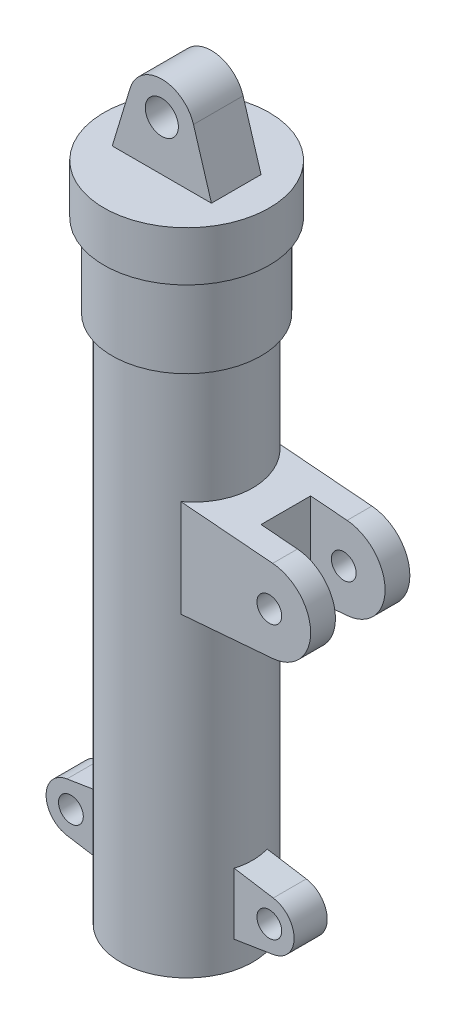
SolidWorks part; units mm, degrees
ref_plane "Front Plane" through (0, 0, 0) normal (0, 0, 1) x (1, 0, 0)
ref_plane "Top Plane" through (0, 0, 0) normal (0, 1, 0) x (1, 0, 0)
ref_plane "Right Plane" through (0, 0, 0) normal (1, 0, 0) x (0, 0, -1)
sketch "Sketch1" plane through (0, 0, 0) normal (0, 0, 1) x (1, 0, 0)
  line L0 (0, -64.3365) -> (0, 400) construction
  line L1 (-103.0806, 0) -> (86.019, 0) construction
  line L2 (0, 400) -> (50, 400)
  line L3 (50, 400) -> (50, 370)
  line L4 (50, 370) -> (45, 370)
  line L5 (45, 370) -> (45, 320)
  line L6 (45, 320) -> (40, 320)
  line L7 (40, 320) -> (40, 0)
  line L8 (40, 0) -> (22.5, 0)
  line L9 (22.5, 0) -> (22.5, 5)
  line L10 (22.5, 5) -> (35, 5)
  line L11 (35, 5) -> (35, 385)
  line L12 (35, 385) -> (0, 385)
  line L13 (0, 385) -> (0, 400)
  point P18 (0, 392.5)
  dimension "D1" = 50
  dimension "D2" = 400
  dimension "D3" = 30
  dimension "D4" = 80
  dimension "D5" = 15
  dimension "D6" = 5
  dimension "D7" = 35
  dimension "D8" = 40
  dimension "D9" = 5
  dimension "D10" = 22.5
revolve "Revolve1" add sketch "Sketch1" angle 360 about L0
sketch "Sketch2" plane through (0, 0, 0) normal (0, 0, 1) x (1, 0, 0)
  line L0 (0, 454.1311) -> (0, 337.0526) construction
  line L1 (-51.2477, 400) -> (111.9982, 400) construction
  line L2 (-30, 400) -> (30, 400)
  line L3 (-30, 400) -> (-19.1389, 435.8055)
  line L4 (30, 400) -> (19.1389, 435.8055)
  arc A0 (19.1389, 435.8055) -> (-19.1389, 435.8055) centre (0, 430) ccw
  circle A1 centre (0, 430) radius 10
  dimension "D1" = 40
  dimension "D6" = 20
  dimension "D2" = 30
  dimension "D3" = 0
  dimension "D4" = 60
  dimension "D5" = 30
extrude "Boss-Extrude1" add sketch "Sketch2" along normal mid plane 30
sketch "Sketch3" plane through (0, 0, 0) normal (0, 0, 1) x (1, 0, 0)
  line L0 (-101.4963, 35) -> (205.3814, 35) construction
  line L1 (-53.1936, 0) -> (61.4102, 0) construction
  line L2 (0, 493.5794) -> (0, -75.5846) construction
  line L3 (30, 15) -> (30, 55)
  line L4 (30, 55) -> (62.374, 49.811)
  line L5 (30, 15) -> (62.374, 20.189)
  arc A0 (62.374, 20.189) -> (62.374, 49.811) centre (60, 35) ccw
  circle A1 centre (60, 35) radius 7.5
  dimension "D1" = 30
  dimension "D8" = 15
  dimension "D2" = 35
  dimension "D3" = 0
  dimension "D4" = 40
  dimension "D5" = 30
  dimension "D6" = 20
  dimension "D7" = 30
extrude "Boss-Extrude2" add sketch "Sketch3" along normal mid plane 20
mirror "Mirror1" about plane through (0, 0, 0) normal (1, 0, 0) of "Boss-Extrude2"
sketch "Sketch4" plane through (0, 0, 0) normal (0, 0, 1) x (1, 0, 0)
  line L0 (-111.3822, 220) -> (186.4856, 220) construction
  line L1 (0, 466.5403) -> (0, -20.3591) construction
  line L2 (0, 320) -> (0, 0) construction
  line L3 (-40, 320) -> (40, 320) construction
  line L4 (20, 250) -> (20, 190)
  line L5 (20, 250) -> (82.0416, 244.9165)
  line L6 (20, 190) -> (82.0416, 195.0835)
  arc A0 (82.0416, 195.0835) -> (82.0416, 244.9165) centre (80, 220) ccw
  circle A1 centre (80, 220) radius 7.5
  point P13 (37.5517, 220)
  dimension "D2" = 50
  dimension "D8" = 15
  dimension "D1" = 100
  dimension "D3" = 0
  dimension "D4" = 60
  dimension "D5" = 20
  dimension "D6" = 30
  dimension "D7" = 60
extrude "Boss-Extrude3" add sketch "Sketch4" along normal mid plane 60
sketch "Sketch5" plane through (0, 0, 0) normal (0, 0, 1) x (1, 0, 0)
  line L1 (60, 260) -> (130, 260)
  line L2 (60, 260) -> (60, 180)
  line L3 (60, 180) -> (130, 180)
  line L4 (130, 260) -> (130, 180)
  circle A0 centre (80, 220) radius 7.5 construction
  dimension "D3" = 40
  dimension "D4" = 20
  dimension "D1" = 70
  dimension "D2" = 80
extrude "Cut-Extrude1" cut sketch "Sketch5" against normal mid plane 30
sketch "Sketch6" plane through (0, 0, 0) normal (0, 0, 1) x (1, 0, 0)
  line L0 (-40, 320) -> (40, 320) construction
  line L1 (35, 320) -> (0, 320)
  line L2 (35, 320) -> (35, 5)
  line L3 (35, 5) -> (0, 5)
  line L4 (0, 320) -> (0, 5)
  line L5 (40, 248.3613) -> (40, 320) construction
  line L6 (-40, 0) -> (40, 0) construction
  dimension "D1" = 0
  dimension "D2" = 5
  dimension "D3" = 35
  dimension "D4" = 5
revolve "Cut-Revolve1" cut sketch "Sketch6" angle 360 about L4
